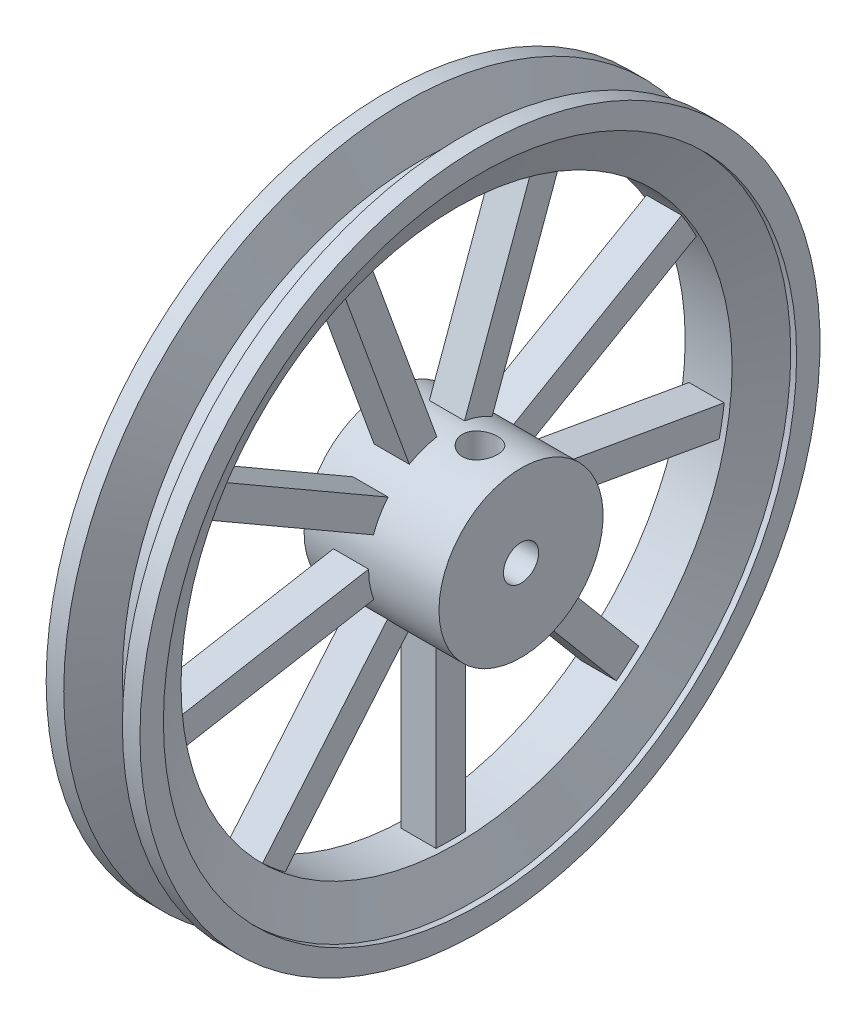
SolidWorks part; units mm, degrees
material "AISI 1020"
ref_plane "Front Plane" through (0, 0, 0) normal (0, 0, 1) x (1, 0, 0)
ref_plane "Top Plane" through (0, 0, 0) normal (0, 1, 0) x (1, 0, 0)
ref_plane "Right Plane" through (0, 0, 0) normal (1, 0, 0) x (0, 0, -1)
sketch "Sketch1" plane through (0, 0, 0) normal (0, 0, 1) x (1, 0, 0)
  line L0 (-229.1101, 0) -> (256.14, 0) construction
  line L1 (47.625, 9.525) -> (-25.4, 9.525)
  line L2 (-25.4, 9.525) -> (-25.4, 44.45)
  line L3 (-25.4, 44.45) -> (-9.525, 44.45)
  line L4 (-9.525, 44.45) -> (-9.525, 149.225)
  line L5 (-9.525, 149.225) -> (-12.7, 149.225)
  line L6 (-12.7, 149.225) -> (-22.225, 171.45)
  line L7 (-22.225, 171.45) -> (-25.4, 171.45)
  line L8 (-25.4, 171.45) -> (-25.4, 184.15)
  line L9 (-25.4, 184.15) -> (-15.875, 184.15)
  line L10 (-15.875, 184.15) -> (-6.35, 161.925)
  line L18 (9.525, 149.225) -> (9.525, 44.45)
  line L19 (9.525, 44.45) -> (47.625, 44.45)
  line L20 (47.625, 44.45) -> (47.625, 9.525)
  line L21 (0, -98.9848) -> (0, 340.576) construction
  line L22 (-9.525, 82.55) -> (9.525, 82.55) construction
  line L23 (-6.35, 161.925) -> (6.35, 161.925)
  line L24 (25.4, 184.15) -> (15.875, 184.15)
  line L25 (25.4, 171.45) -> (25.4, 184.15)
  line L26 (9.525, 149.225) -> (12.7, 149.225)
  line L27 (15.875, 184.15) -> (6.35, 161.925)
  line L28 (22.225, 171.45) -> (25.4, 171.45)
  line L29 (12.7, 149.225) -> (22.225, 171.45)
  point P27 (0, 82.55)
  point P28 (0, 161.925)
  dimension "D1" = 73.025
  dimension "D4" = 19.05
  dimension "D5" = 88.9
  dimension "D6" = 19.05
  dimension "D3" = 104.775
  dimension "D7" = 117.475
  dimension "D8" = 127
  dimension "D9" = 139.7
  dimension "D10" = 31.75
  dimension "D11" = 50.8
  dimension "D12" = 12.7
  dimension "D13" = 44.45
  dimension "D14" = 38.1
  dimension "D2" = 15.875
revolve "Revolve2" add sketch "Sketch1" angle 360 about L0
sketch "Sketch2" plane through (9.525, 0, 0) normal (1, 0, 0) x (0, 0, -1)
  line L0 (0, 0) -> (-123.9218, 340.4724) construction
  line L1 (0, 0) -> (0, 356.8073) construction
  line L2 (0, 0) -> (131.6911, 361.8185) construction
  line L3 (-7.4996, 43.8128) -> (-43.5069, 142.7419)
  line L4 (7.4996, 43.8128) -> (43.5069, 142.7419)
  circle A0 centre (0, 0) radius 44.45 construction
  circle A1 centre (0, 0) radius 149.225 construction
  circle A2 centre (0, 0) radius 149.225 construction
  arc A3 (43.5069, 142.7419) -> (-43.5069, 142.7419) centre (0, 0) ccw
  circle A4 centre (0, 0) radius 44.45 construction
  arc A5 (7.4996, 43.8128) -> (-7.4996, 43.8128) centre (0, 0) ccw
  dimension "D1" = 20
  dimension "D2" = 40
  dimension "D3" = 15.875
  dimension "D4" = 15.875
extrude "Cut-Extrude1" cut sketch "Sketch2" against normal through all
pattern_circular "CirPattern2" count 9 over 360 about axis through (0, 0, 0) along (1, 0, 0) of "Cut-Extrude1"
ref_plane "Plane1" through (0, 44.45, 0) normal (0, 1, 0) x (1, 0, 0)
sketch "Sketch3" plane through (0, 44.45, 0) normal (0, 1, 0) x (1, 0, 0)
  line L0 (47.625, 0) -> (-25.4, 0) construction
  circle A0 centre (25.4, 0) radius 9.525
  dimension "D1" = 19.05
  dimension "D2" = 25.4
extrude "Cut-Extrude2" cut sketch "Sketch3" against normal up to surface (44.45 mm away)
equation "\"A\"= .75"
equation "\"B\"= 3.5"
equation "\"D5@Sketch1\"=\"B\""
equation "\"D6@Sketch1\"=\"A\""
